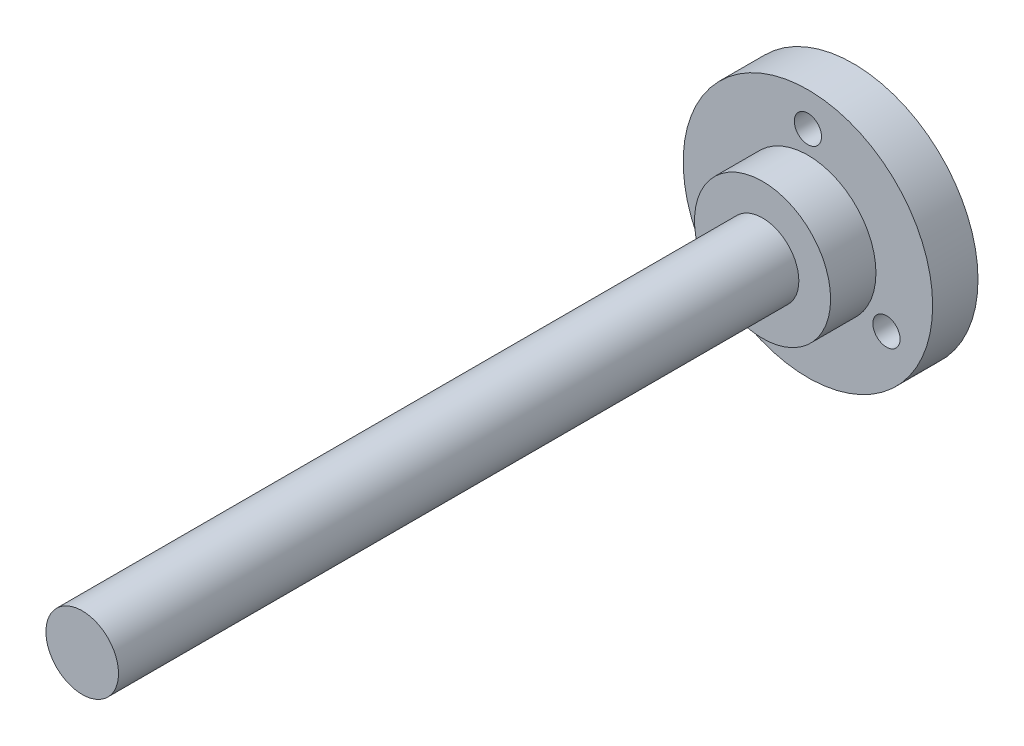
SolidWorks part; units mm, degrees
ref_plane "Front Plane" through (0, 0, 0) normal (0, 0, 1) x (1, 0, 0)
ref_plane "Top Plane" through (0, 0, 0) normal (0, 1, 0) x (1, 0, 0)
ref_plane "Right Plane" through (0, 0, 0) normal (1, 0, 0) x (0, 0, -1)
sketch "Sketch1" plane through (0, 0, 0) normal (0, 0, 1) x (1, 0, 0)
  circle A0 centre (0, 0) radius 27.5
  circle A1 centre (0, 20) radius 3
  circle A2 centre (17.3205, -10) radius 3
  circle A3 centre (-17.3205, -10) radius 3
  dimension "D1" = 55
  dimension "D2" = 6
  dimension "D4" = 20
  dimension "D3" = 3
extrude "Boss-Extrude1" add sketch "Sketch1" along normal blind 10
sketch "Sketch2" plane through (0, 0, 10) normal (0, 0, 1) x (1, 0, 0)
  circle A0 centre (0, 0) radius 15
  dimension "D1" = 30
extrude "Boss-Extrude2" add sketch "Sketch2" along normal blind 10
sketch "Sketch3" plane through (0, 0, 20) normal (0, 0, 1) x (1, 0, 0)
  circle A0 centre (0, 0) radius 8
  dimension "D1" = 16
extrude "Boss-Extrude3" add sketch "Sketch3" along normal blind 150
